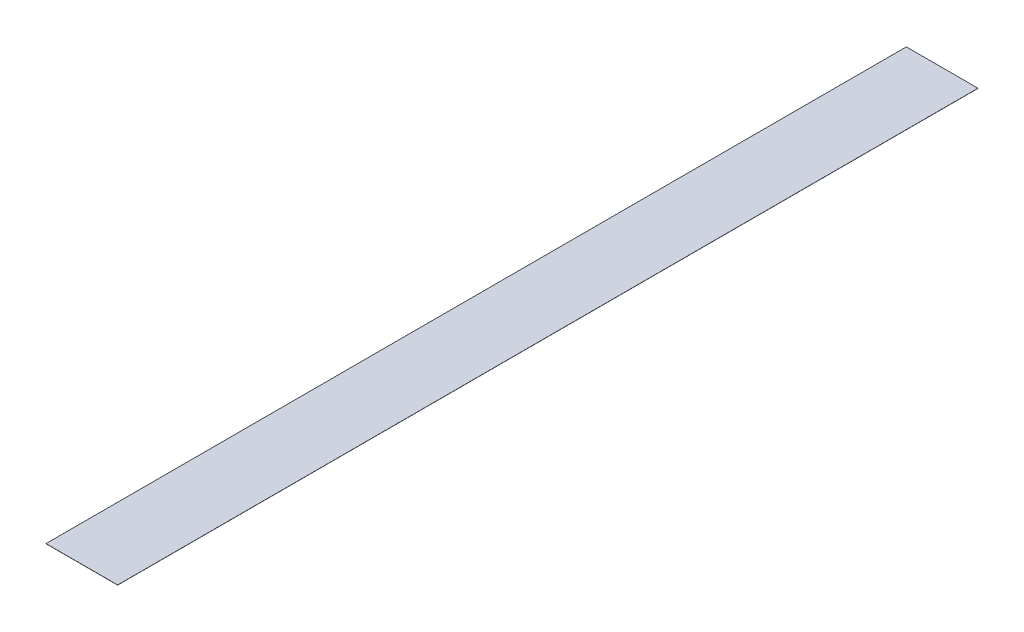
SolidWorks part; units mm, degrees
material "acrylic adhesive"
ref_plane "Front" through (0, 0, 0) normal (0, 0, 1) x (1, 0, 0)
ref_plane "Top" through (0, 0, 0) normal (0, 1, 0) x (1, 0, 0)
ref_plane "Right" through (0, 0, 0) normal (1, 0, 0) x (0, 0, -1)
sketch "Sketch1" plane through (0, 0, 0) normal (0, 1, 0) x (1, 0, 0)
  line L0 (12.45, 149.5) -> (-12.45, -149.5) construction
  line L1 (-12.45, 149.5) -> (12.45, 149.5)
  line L2 (-12.45, 149.5) -> (-12.45, -149.5)
  line L3 (-12.45, -149.5) -> (12.45, -149.5)
  line L4 (12.45, 149.5) -> (12.45, -149.5)
  point P4 (0, 0)
  dimension "D1" = 299
  dimension "D2" = 24.9
extrude "Extrude1" add sketch "Sketch1" along normal blind 0.0508
